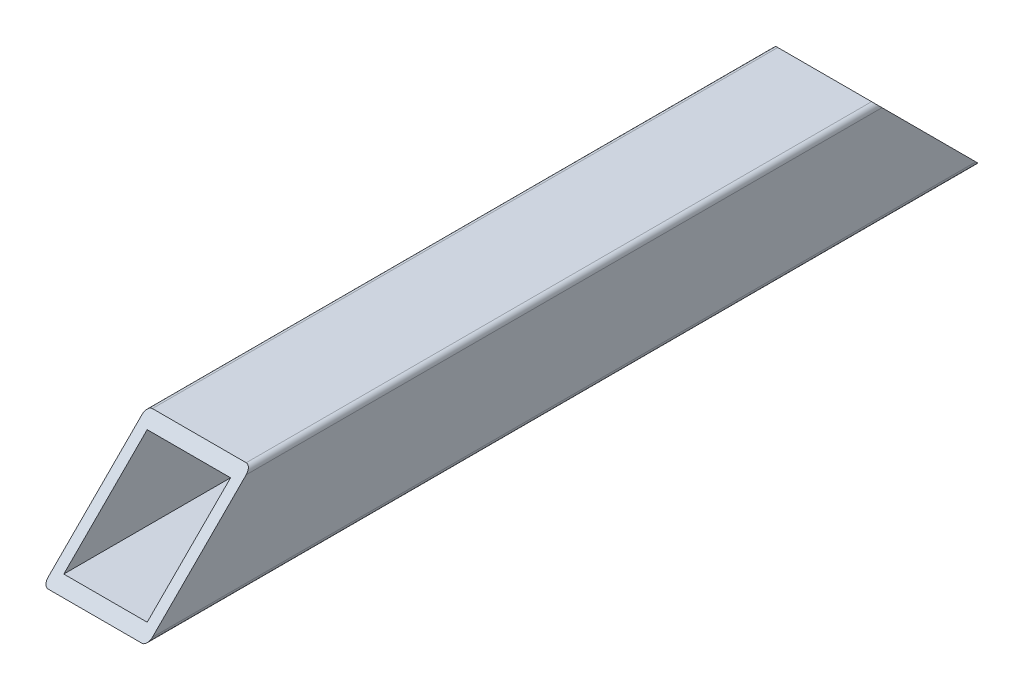
SolidWorks part; units mm, degrees
ref_plane "前视基准面" through (0, 0, 0) normal (0, 0, 1) x (1, 0, 0)
ref_plane "上视基准面" through (0, 0, 0) normal (0, 1, 0) x (1, 0, 0)
ref_plane "右视基准面" through (0, 0, 0) normal (1, 0, 0) x (0, 0, -1)
sketch "草图1" plane through (0, 0, 0) normal (1, 0, 0) x (0, 0, -1)
  line L0 (0, 0) -> (80, 0)
  dimension "D1" = 80
other "自定义型材 不锈钢10×10(1)"
ref_plane "基准面1" through (0, 0, 0) normal (0, 0, -1) x (0, 1, 0)
sketch "草图11" plane through (0, 0, 0) normal (0, 0, -1) x (0, 1, 0)
  line L0 (-4, -4) -> (-4, 4)
  line L1 (-4.5, -5) -> (4.5, -5)
  line L2 (-5, -4.5) -> (-5, 4.5)
  line L3 (-4.5, 5) -> (4.5, 5)
  line L4 (5, -4.5) -> (5, 4.5)
  line L5 (-5, -5) -> (5, 5) construction
  line L6 (-5, 5) -> (5, -5) construction
  line L7 (-4, 4) -> (4, 4)
  line L8 (4, -4) -> (4, 4)
  line L9 (-4, -4) -> (4, -4)
  line L10 (0, 5) -> (0, 4) construction
  line L11 (0, -4) -> (0, -5) construction
  line L12 (-5, 0) -> (5, 0) construction
  line L13 (-5, 0) -> (-10, 0) construction
  line L14 (-10, 0) -> (-25, 0) construction
  line L15 (5, 0) -> (10, 0) construction
  line L16 (10, 0) -> (25, 0) construction
  arc A0 (4.5, -5) -> (5, -4.5) centre (4.5, -4.5) ccw
  arc A1 (-5, -4.5) -> (-4.5, -5) centre (-4.5, -4.5) ccw
  arc A2 (4.5, 5) -> (5, 4.5) centre (4.5, 4.5) cw
  arc A3 (-5, 4.5) -> (-4.5, 5) centre (-4.5, 4.5) cw
  arc A4 (-4, 4) -> (-4, 4) centre (-4, 4) cw
  arc A5 (4, 4) -> (4, 4) centre (4, 4) cw
  arc A6 (4, -4) -> (4, -4) centre (4, -4) ccw
  arc A7 (-4, -4) -> (-4, -4) centre (-4, -4) ccw
  point P0 (0, 0)
  point P36 (0, 0)
  dimension "D3" = 0.5
  dimension "D1" = 10
  dimension "D2" = 10
  dimension "D5" = 5
  dimension "D6" = 15
  dimension "D4" = 1
sketch "草图12" plane through (0, 0, 0) normal (1, 0, 0) x (0, 0, -1)
  line L0 (0, -5) -> (0, 5)
  line L1 (0, 5) -> (10, 5)
  line L2 (80, 5) -> (0, 5) construction
  line L3 (10, 5) -> (0, -5)
  line L4 (80, -5) -> (80, 5)
  line L5 (80, 5) -> (70, 5)
  line L6 (70, 5) -> (80, -5)
extrude "切除-拉伸1" cut sketch "草图12" against normal mid plane 10
